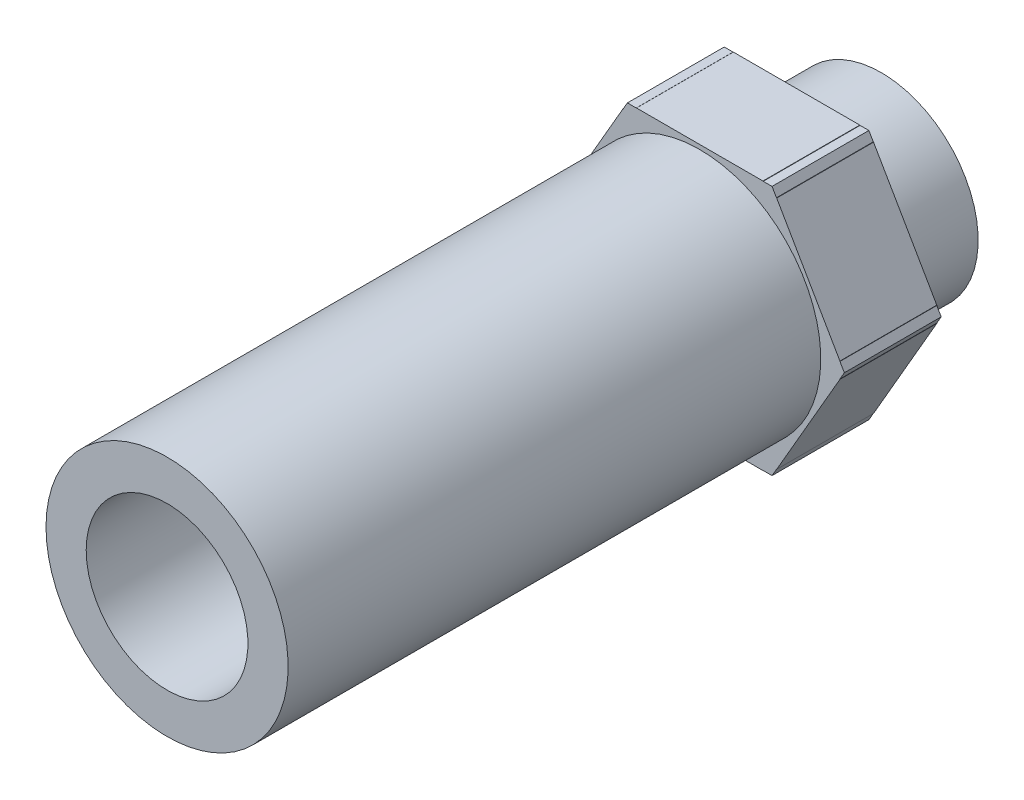
SolidWorks part; units mm, degrees
ref_plane "Alzado" through (0, 0, 0) normal (0, 0, 1) x (1, 0, 0)
ref_plane "Planta" through (0, 0, 0) normal (0, 1, 0) x (1, 0, 0)
ref_plane "Vista lateral" through (0, 0, 0) normal (1, 0, 0) x (0, 0, -1)
sketch "Croquis1" plane through (0, 0, 0) normal (0, 1, 0) x (1, 0, 0)
  line L0 (0, 40.16) -> (0, -130) construction
  line L1 (16.7, -87.44) -> (16.7, 17.5)
  line L2 (16.7, 17.5) -> (20, 17.5)
  line L3 (20, 17.5) -> (20, 0)
  line L4 (20, 0) -> (29, 0)
  line L5 (29, 0) -> (29, -20)
  line L6 (29, -20) -> (25, -20)
  line L7 (25, -20) -> (25, -130)
  line L8 (25, -130) -> (16.7, -130)
  line L9 (16.7, -130) -> (16.7, -87.44)
  dimension "D1" = 20
  dimension "D2" = 17.5
  dimension "D3" = 20
  dimension "D4" = 110
  dimension "D5" = 25
  dimension "D6" = 29
  dimension "D7" = 16.7
revolve "Revolución1" add sketch "Croquis1" angle 360 about L0
sketch "Croquis3" plane through (0, 0, 0) normal (0, 0, 1) x (1, 0, 0)
  line L1 (29.8669, 0) -> (14.9335, 25.8655)
  line L2 (14.9335, 25.8655) -> (-14.9335, 25.8655)
  line L3 (-14.9335, 25.8655) -> (-29.8669, 0)
  line L4 (-29.8669, 0) -> (-14.9335, -25.8655)
  line L5 (-14.9335, -25.8655) -> (14.9335, -25.8655)
  line L6 (14.9335, -25.8655) -> (29.8669, 0)
  circle A0 centre (0, 0) radius 25.8655 construction
extrude "Saliente-Extruir1" add sketch "Croquis3" along normal blind 20
sketch "Croquis4" plane through (0, 0, 0) normal (0, 0, 1) x (1, 0, 0)
  line L1 (29.8995, 0) -> (14.9498, 25.8938)
  line L2 (14.9498, 25.8938) -> (-14.9498, 25.8938)
  line L3 (-14.9498, 25.8938) -> (-29.8995, 0)
  line L4 (-29.8995, 0) -> (-14.9498, -25.8938)
  line L5 (-14.9498, -25.8938) -> (14.9498, -25.8938)
  line L6 (14.9498, -25.8938) -> (29.8995, 0)
  circle A0 centre (0, 0) radius 25.8938 construction
extrude "Cortar-Extruir3" cut sketch "Croquis4" along normal blind 20 flip side to cut
sketch "Croquis5" plane through (0, 0, 0) normal (0, 0, 1) x (1, 0, 0)
  circle A0 centre (0, 0) radius 16.7
  circle A1 centre (0, 0) radius 16.7
